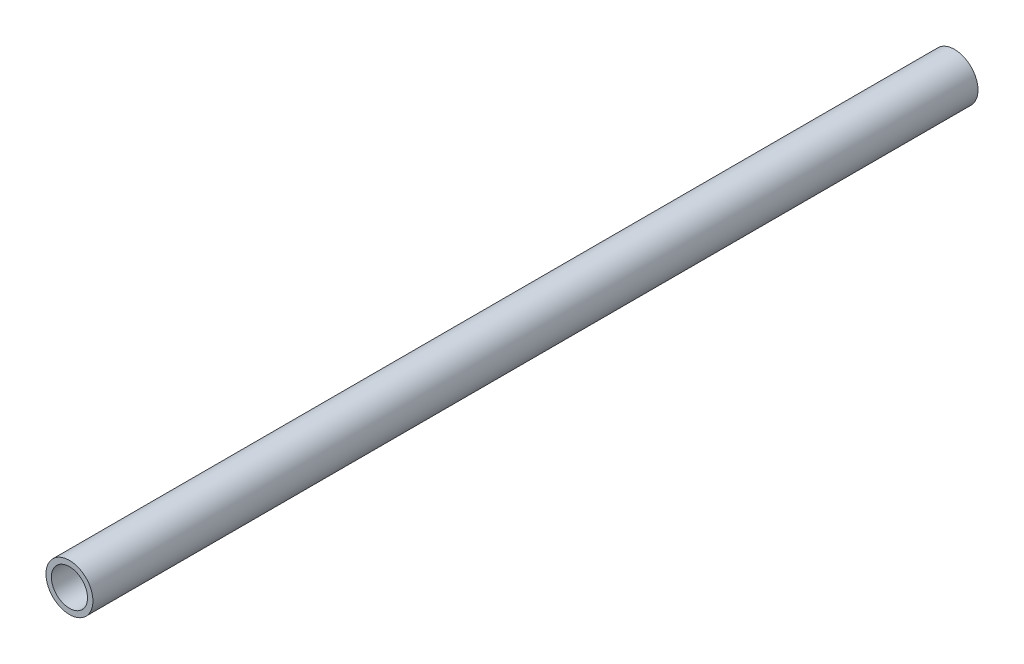
SolidWorks part; units mm, degrees
ref_plane "Front Plane" through (0, 0, 0) normal (0, 0, 1) x (1, 0, 0)
ref_plane "Top Plane" through (0, 0, 0) normal (0, 1, 0) x (1, 0, 0)
ref_plane "Right Plane" through (0, 0, 0) normal (1, 0, 0) x (0, 0, -1)
sketch "Sketch1" plane through (0, 0, 0) normal (0, 0, 1) x (1, 0, 0)
  circle A0 centre (0, 0) radius 6.5
  dimension "D1" = 13
extrude "Extrude-Thin1" add sketch "Sketch1" along normal blind 245 thin thin type one direction reverse wall 1.5
